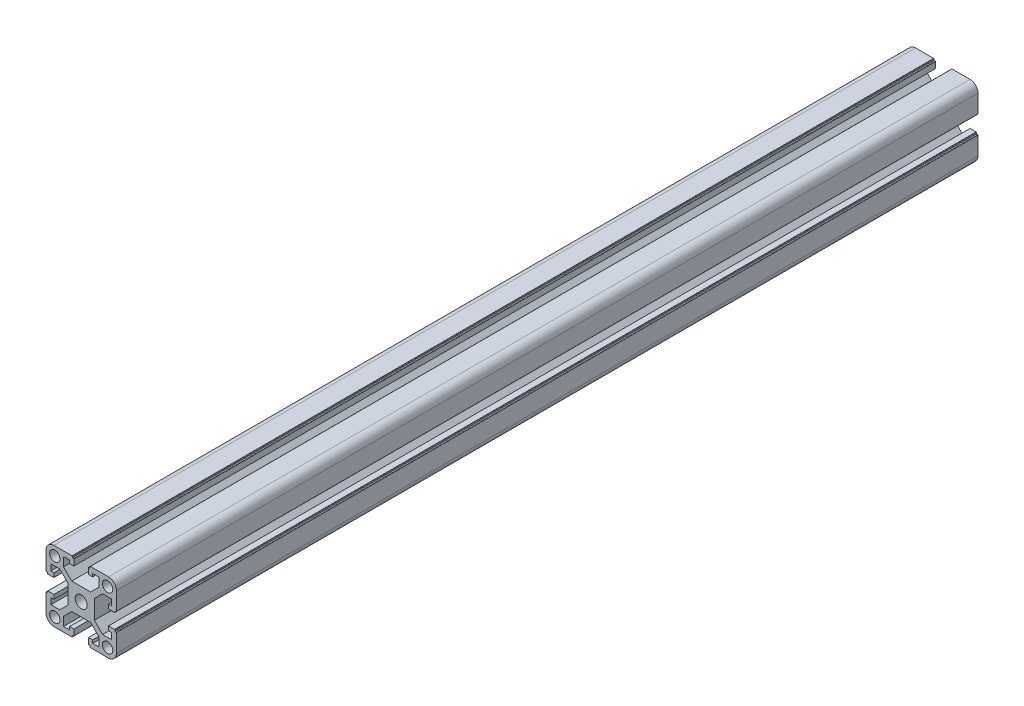
SolidWorks part; units mm, degrees
material "6061-T6 (SS)"
ref_plane "前视基准面" through (0, 0, 0) normal (0, 0, 1) x (1, 0, 0)
ref_plane "上视基准面" through (0, 0, 0) normal (0, 1, 0) x (1, 0, 0)
ref_plane "右视基准面" through (0, 0, 0) normal (1, 0, 0) x (0, 0, -1)
ref_plane "基准面1" through (0, 0, 100) normal (0, 0, 1) x (1, 0, 0)
sketch "草图1" plane through (0, 0, 100) normal (0, 0, 1) x (1, 0, 0)
  line L0 (-1518.245, 3588.0043) -> (-1518.245, 3582.9756)
  line L1 (-1518.245, 3582.9756) -> (-1522.9163, 3578.3043)
  line L2 (-1522.9163, 3578.3043) -> (-1533.6737, 3578.3043)
  line L3 (-1533.6737, 3578.3043) -> (-1538.345, 3582.9756)
  line L4 (-1538.345, 3582.9756) -> (-1538.345, 3588.0043)
  line L5 (-1538.345, 3588.0043) -> (-1534.845, 3588.0043)
  line L6 (-1534.845, 3588.0043) -> (-1534.845, 3586.3043)
  line L7 (-1534.845, 3586.3043) -> (-1532.445, 3586.3043)
  line L8 (-1532.445, 3586.3043) -> (-1532.445, 3589.7043)
  line L9 (-1532.645, 3589.9043) -> (-1533.345, 3589.9043)
  line L10 (-1533.345, 3589.9043) -> (-1533.345, 3590.6043)
  line L11 (-1533.545, 3590.8043) -> (-1543.795, 3590.8043)
  line L12 (-1548.295, 3586.3043) -> (-1548.295, 3576.0543)
  line L13 (-1548.095, 3575.8543) -> (-1547.395, 3575.8543)
  line L14 (-1547.395, 3575.8543) -> (-1547.395, 3575.1543)
  line L15 (-1547.195, 3574.9543) -> (-1543.795, 3574.9543)
  line L16 (-1543.795, 3574.9543) -> (-1543.795, 3577.3543)
  line L17 (-1543.795, 3577.3543) -> (-1545.495, 3577.3543)
  line L18 (-1545.495, 3577.3543) -> (-1545.495, 3580.8543)
  line L19 (-1545.495, 3580.8543) -> (-1540.4663, 3580.8543)
  line L20 (-1540.4663, 3580.8543) -> (-1535.795, 3576.183)
  line L21 (-1535.795, 3576.183) -> (-1535.795, 3565.4256)
  line L22 (-1535.795, 3565.4256) -> (-1540.4663, 3560.7543)
  line L23 (-1540.4663, 3560.7543) -> (-1545.495, 3560.7543)
  line L24 (-1545.495, 3560.7543) -> (-1545.495, 3564.2543)
  line L25 (-1545.495, 3564.2543) -> (-1543.795, 3564.2543)
  line L26 (-1543.795, 3564.2543) -> (-1543.795, 3566.6543)
  line L27 (-1543.795, 3566.6543) -> (-1547.195, 3566.6543)
  line L28 (-1547.395, 3566.4543) -> (-1547.395, 3565.7543)
  line L29 (-1547.395, 3565.7543) -> (-1548.095, 3565.7543)
  line L30 (-1548.295, 3565.5543) -> (-1548.295, 3555.3043)
  line L31 (-1543.795, 3550.8043) -> (-1533.545, 3550.8043)
  line L32 (-1533.345, 3551.0043) -> (-1533.345, 3551.7043)
  line L33 (-1533.345, 3551.7043) -> (-1532.645, 3551.7043)
  line L34 (-1532.445, 3551.9043) -> (-1532.445, 3555.3043)
  line L35 (-1532.445, 3555.3043) -> (-1534.845, 3555.3043)
  line L36 (-1534.845, 3555.3043) -> (-1534.845, 3553.6043)
  line L37 (-1534.845, 3553.6043) -> (-1538.345, 3553.6043)
  line L38 (-1538.345, 3553.6043) -> (-1538.345, 3558.633)
  line L39 (-1538.345, 3558.633) -> (-1533.6737, 3563.3043)
  line L40 (-1533.6737, 3563.3043) -> (-1522.9163, 3563.3043)
  line L41 (-1522.9163, 3563.3043) -> (-1518.245, 3558.633)
  line L42 (-1518.245, 3558.633) -> (-1518.245, 3553.6043)
  line L43 (-1518.245, 3553.6043) -> (-1521.745, 3553.6043)
  line L44 (-1521.745, 3553.6043) -> (-1521.745, 3555.3043)
  line L45 (-1521.745, 3555.3043) -> (-1524.145, 3555.3043)
  line L46 (-1524.145, 3555.3043) -> (-1524.145, 3551.9043)
  line L47 (-1523.945, 3551.7043) -> (-1523.245, 3551.7043)
  line L48 (-1523.245, 3551.7043) -> (-1523.245, 3551.0043)
  line L49 (-1523.045, 3550.8043) -> (-1512.795, 3550.8043)
  line L50 (-1508.295, 3555.3043) -> (-1508.295, 3565.5543)
  line L51 (-1508.495, 3565.7543) -> (-1509.195, 3565.7543)
  line L52 (-1509.195, 3565.7543) -> (-1509.195, 3566.4543)
  line L53 (-1509.395, 3566.6543) -> (-1512.795, 3566.6543)
  line L54 (-1512.795, 3566.6543) -> (-1512.795, 3564.2543)
  line L55 (-1512.795, 3564.2543) -> (-1511.095, 3564.2543)
  line L56 (-1511.095, 3564.2543) -> (-1511.095, 3560.7543)
  line L57 (-1511.095, 3560.7543) -> (-1516.1237, 3560.7543)
  line L58 (-1516.1237, 3560.7543) -> (-1520.795, 3565.4256)
  line L59 (-1520.795, 3565.4256) -> (-1520.795, 3576.183)
  line L60 (-1520.795, 3576.183) -> (-1516.1237, 3580.8543)
  line L61 (-1516.1237, 3580.8543) -> (-1511.095, 3580.8543)
  line L62 (-1511.095, 3580.8543) -> (-1511.095, 3577.3543)
  line L63 (-1511.095, 3577.3543) -> (-1512.795, 3577.3543)
  line L64 (-1512.795, 3577.3543) -> (-1512.795, 3574.9543)
  line L65 (-1512.795, 3574.9543) -> (-1509.395, 3574.9543)
  line L66 (-1509.195, 3575.1543) -> (-1509.195, 3575.8543)
  line L67 (-1509.195, 3575.8543) -> (-1508.495, 3575.8543)
  line L68 (-1508.295, 3576.0543) -> (-1508.295, 3586.3043)
  line L69 (-1512.795, 3590.8043) -> (-1523.045, 3590.8043)
  line L70 (-1523.245, 3590.6043) -> (-1523.245, 3589.9043)
  line L71 (-1523.245, 3589.9043) -> (-1523.945, 3589.9043)
  line L72 (-1524.145, 3589.7043) -> (-1524.145, 3586.3043)
  line L73 (-1524.145, 3586.3043) -> (-1521.745, 3586.3043)
  line L74 (-1521.745, 3586.3043) -> (-1521.745, 3588.0043)
  line L75 (-1521.745, 3588.0043) -> (-1518.245, 3588.0043)
  circle A0 centre (-1513.27, 3555.7793) radius 2.95
  circle A1 centre (-1528.295, 3570.8043) radius 3.4
  circle A2 centre (-1513.27, 3585.8293) radius 2.95
  arc A3 (-1532.445, 3589.7043) -> (-1532.645, 3589.9043) centre (-1532.645, 3589.7043) ccw
  arc A4 (-1533.345, 3590.6043) -> (-1533.545, 3590.8043) centre (-1533.545, 3590.6043) ccw
  arc A5 (-1543.795, 3590.8043) -> (-1548.295, 3586.3043) centre (-1543.795, 3586.3043) ccw
  arc A6 (-1548.295, 3576.0543) -> (-1548.095, 3575.8543) centre (-1548.095, 3576.0543) ccw
  arc A7 (-1547.395, 3575.1543) -> (-1547.195, 3574.9543) centre (-1547.195, 3575.1543) ccw
  arc A8 (-1547.195, 3566.6543) -> (-1547.395, 3566.4543) centre (-1547.195, 3566.4543) ccw
  arc A9 (-1548.095, 3565.7543) -> (-1548.295, 3565.5543) centre (-1548.095, 3565.5543) ccw
  arc A10 (-1548.295, 3555.3043) -> (-1543.795, 3550.8043) centre (-1543.795, 3555.3043) ccw
  arc A11 (-1533.545, 3550.8043) -> (-1533.345, 3551.0043) centre (-1533.545, 3551.0043) ccw
  arc A12 (-1532.645, 3551.7043) -> (-1532.445, 3551.9043) centre (-1532.645, 3551.9043) ccw
  arc A13 (-1524.145, 3551.9043) -> (-1523.945, 3551.7043) centre (-1523.945, 3551.9043) ccw
  arc A14 (-1523.245, 3551.0043) -> (-1523.045, 3550.8043) centre (-1523.045, 3551.0043) ccw
  arc A15 (-1512.795, 3550.8043) -> (-1508.295, 3555.3043) centre (-1512.795, 3555.3043) ccw
  arc A16 (-1508.295, 3565.5543) -> (-1508.495, 3565.7543) centre (-1508.495, 3565.5543) ccw
  arc A17 (-1509.195, 3566.4543) -> (-1509.395, 3566.6543) centre (-1509.395, 3566.4543) ccw
  arc A18 (-1509.395, 3574.9543) -> (-1509.195, 3575.1543) centre (-1509.395, 3575.1543) ccw
  arc A19 (-1508.495, 3575.8543) -> (-1508.295, 3576.0543) centre (-1508.495, 3576.0543) ccw
  arc A20 (-1508.295, 3586.3043) -> (-1512.795, 3590.8043) centre (-1512.795, 3586.3043) ccw
  arc A21 (-1523.045, 3590.8043) -> (-1523.245, 3590.6043) centre (-1523.045, 3590.6043) ccw
  arc A22 (-1523.945, 3589.9043) -> (-1524.145, 3589.7043) centre (-1523.945, 3589.7043) ccw
  circle A23 centre (-1543.32, 3585.8293) radius 2.95
  circle A24 centre (-1543.32, 3555.7793) radius 2.95
extrude "凸台-拉伸1" add sketch "草图1" against normal mid plane 490
ref_plane "基准面2" through (-1528.295, 0, 0) normal (1, 0, 0) x (0, 0, -1)
ref_plane "基准面3" through (0, 3570.8043, 0) normal (0, 1, 0) x (1, 0, 0)
sketch "草图2" plane through (0, 3578.3043, 0) normal (0, 1, 0) x (1, 0, 0)
  line L0 (-1528.295, 175.2741) -> (-1528.295, -100) construction
  line L1 (-1528.295, -5.6375) -> (-1528.295, 5.6375) construction
  line L2 (-1543.795, -100) -> (-1528.295, -100) construction
  line L4 (-1543.795, 145) -> (-1543.795, -345) construction
  circle A0 centre (-1528.295, 15) radius 4
  circle A1 centre (-1528.295, -215) radius 4
  dimension "D1" = 8
  dimension "D2" = 115
extrude "切除-拉伸1" cut sketch "草图2" against normal blind 49
